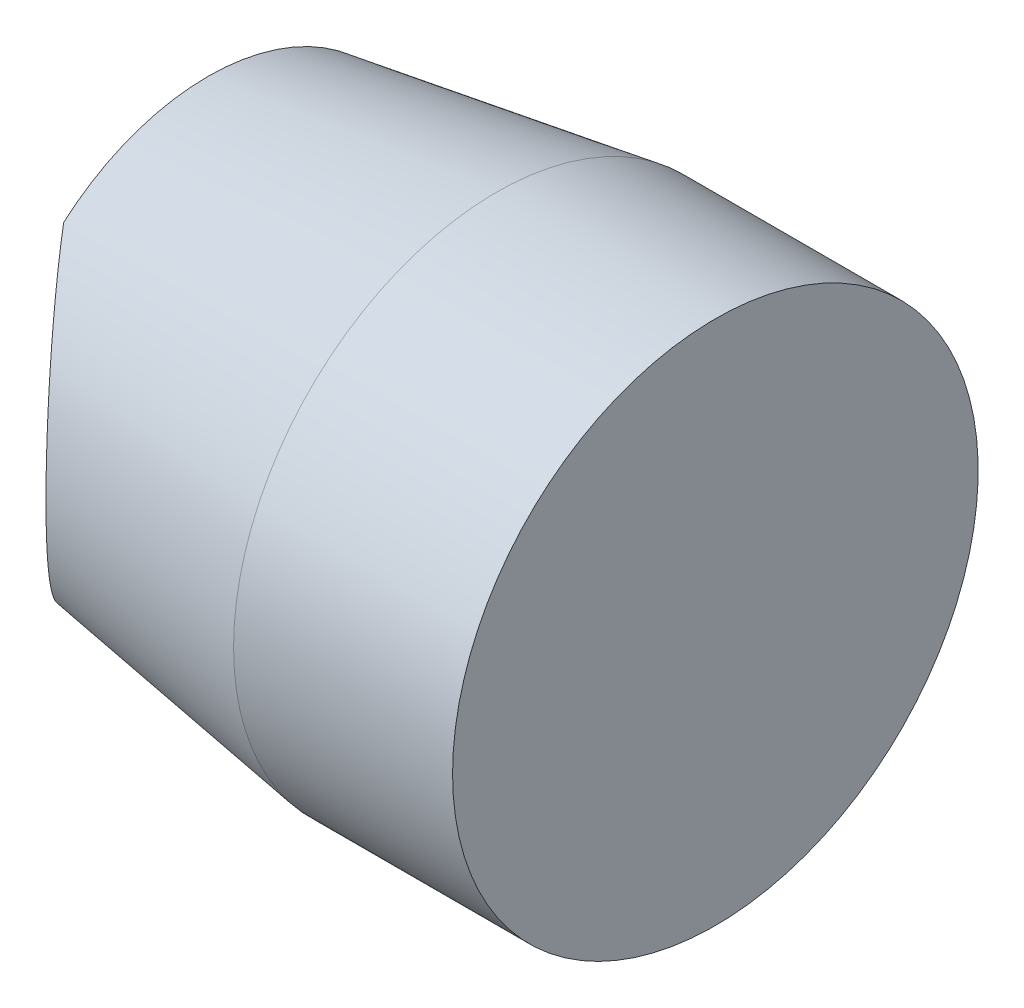
SolidWorks part; units mm, degrees
ref_plane "Alzado" through (0, 0, 0) normal (0, 0, 1) x (1, 0, 0)
ref_plane "Planta" through (0, 0, 0) normal (0, 1, 0) x (1, 0, 0)
ref_plane "Vista lateral" through (0, 0, 0) normal (1, 0, 0) x (0, 0, -1)
sketch "Croquis1" plane through (0, 0, 0) normal (0, 0, 1) x (1, 0, 0)
  line L0 (0, 0) -> (6.95, 0)
  line L1 (6.95, 0) -> (6.95, 3.6)
  line L2 (6.95, 3.6) -> (3.95, 3.6)
  line L3 (3.95, 3.6) -> (0, 3)
  line L4 (0, 3) -> (0, 0)
  dimension "D1" = 3.6
  dimension "D2" = 3
  dimension "D3" = 3.95
  dimension "D4" = 3
revolve "Revolución1" add sketch "Croquis1" angle 360 about L0
sketch "Croquis2" plane through (0, 0, 0) normal (0, 0, 1) x (1, 0, 0)
  line L0 (-37, 2.5691) -> (-37, -2.4825) construction
  circle A0 centre (-2, 0) radius 3.05
  point P5 (0, 0)
  dimension "D2" = 6.1
  dimension "D1" = 37
  dimension "D3" = 2
revolve "Cortar-Revolución1" cut sketch "Croquis2" angle 360 about L0
